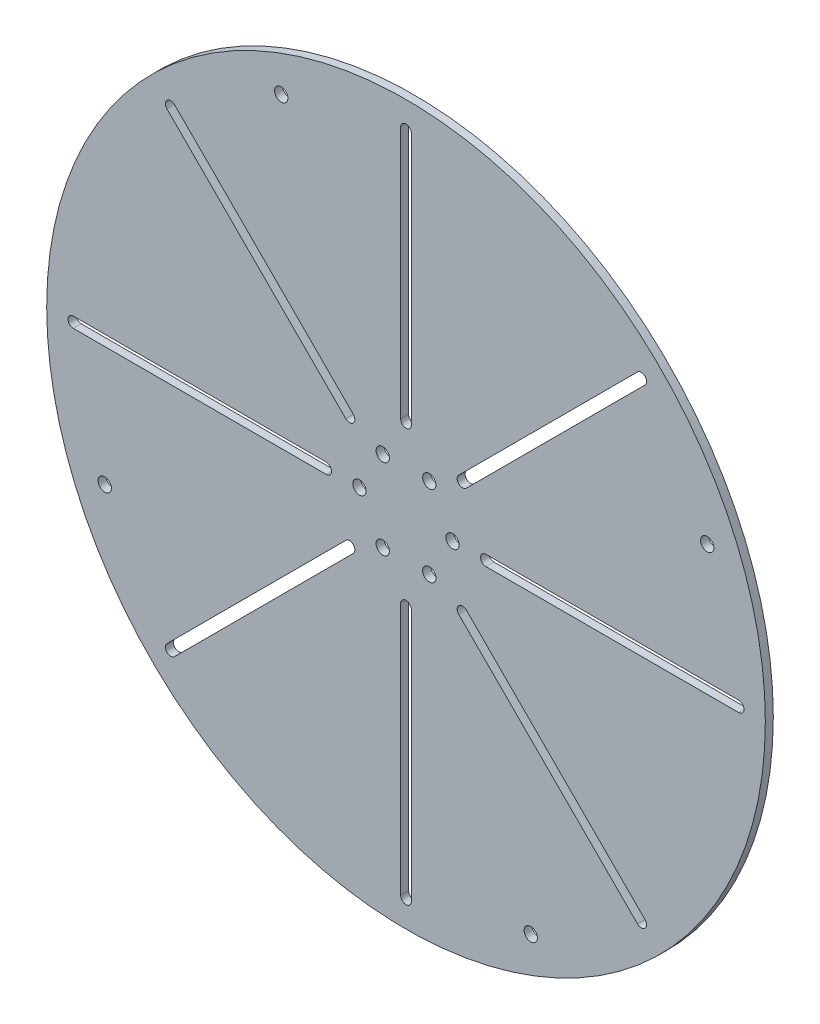
SolidWorks part; units mm, degrees
ref_plane "Front Plane" through (0, 0, 0) normal (0, 0, 1) x (1, 0, 0)
ref_plane "Top Plane" through (0, 0, 0) normal (0, 1, 0) x (1, 0, 0)
ref_plane "Right Plane" through (0, 0, 0) normal (1, 0, 0) x (0, 0, -1)
sketch "Sketch1" plane through (0, 0, 0) normal (0, 0, 1) x (1, 0, 0)
  line L0 (0, 0) -> (125, 0) construction
  line L1 (30, 0) -> (125, 0) construction
  line L2 (30, 2) -> (125, 2)
  line L3 (30, -2) -> (125, -2)
  line L4 (21.2132, -21.2132) -> (88.3883, -88.3883) construction
  line L5 (22.6274, -19.799) -> (89.8026, -86.9741)
  line L6 (19.799, -22.6274) -> (86.9741, -89.8026)
  line L7 (0, -30) -> (0, -125) construction
  line L8 (2, -30) -> (2, -125)
  line L9 (-2, -30) -> (-2, -125)
  line L10 (-21.2132, -21.2132) -> (-88.3883, -88.3883) construction
  line L11 (-19.799, -22.6274) -> (-86.9741, -89.8026)
  line L12 (-22.6274, -19.799) -> (-89.8026, -86.9741)
  line L13 (-30, 0) -> (-125, 0) construction
  line L14 (-30, -2) -> (-125, -2)
  line L15 (-30, 2) -> (-125, 2)
  line L16 (-21.2132, 21.2132) -> (-88.3883, 88.3883) construction
  line L17 (-22.6274, 19.799) -> (-89.8026, 86.9741)
  line L18 (-19.799, 22.6274) -> (-86.9741, 89.8026)
  line L19 (0, 30) -> (0, 125) construction
  line L20 (-2, 30) -> (-2, 125)
  line L21 (2, 30) -> (2, 125)
  line L22 (21.2132, 21.2132) -> (88.3883, 88.3883) construction
  line L23 (19.799, 22.6274) -> (86.9741, 89.8026)
  line L24 (22.6274, 19.799) -> (89.8026, 86.9741)
  line L25 (125, 0) -> (132.5, 0) construction
  line L26 (0, 0) -> (-47.8354, 115.4849) construction
  line L27 (0, 0) -> (0, -15) construction
  circle A0 centre (0, 0) radius 135
  circle A1 centre (0, 0) radius 132.5 construction
  circle A2 centre (0, 0) radius 30 construction
  circle A4 centre (0, 0) radius 125 construction
  arc A5 (30, 2) -> (30, -2) centre (30, 0) ccw
  arc A6 (125, -2) -> (125, 2) centre (125, 0) ccw
  arc A7 (22.6274, -19.799) -> (19.799, -22.6274) centre (21.2132, -21.2132) ccw
  arc A8 (86.9741, -89.8026) -> (89.8026, -86.9741) centre (88.3883, -88.3883) ccw
  arc A9 (2, -30) -> (-2, -30) centre (0, -30) ccw
  arc A10 (-2, -125) -> (2, -125) centre (0, -125) ccw
  arc A11 (-19.799, -22.6274) -> (-22.6274, -19.799) centre (-21.2132, -21.2132) ccw
  arc A12 (-89.8026, -86.9741) -> (-86.9741, -89.8026) centre (-88.3883, -88.3883) ccw
  arc A13 (-30, -2) -> (-30, 2) centre (-30, 0) ccw
  arc A14 (-125, 2) -> (-125, -2) centre (-125, 0) ccw
  arc A15 (-22.6274, 19.799) -> (-19.799, 22.6274) centre (-21.2132, 21.2132) ccw
  arc A16 (-86.9741, 89.8026) -> (-89.8026, 86.9741) centre (-88.3883, 88.3883) ccw
  arc A17 (-2, 30) -> (2, 30) centre (0, 30) ccw
  arc A18 (2, 125) -> (-2, 125) centre (0, 125) ccw
  arc A19 (19.799, 22.6274) -> (22.6274, 19.799) centre (21.2132, 21.2132) ccw
  arc A20 (89.8026, 86.9741) -> (86.9741, 89.8026) centre (88.3883, 88.3883) ccw
  circle A27 centre (0, 0) radius 17.5 construction
  circle A31 centre (-17.5, 0) radius 2.5
  circle A35 centre (-46.8787, 113.1752) radius 2.5
  circle A36 centre (113.1752, 46.8787) radius 2.5
  circle A37 centre (46.8787, -113.1752) radius 2.5
  circle A38 centre (0, 0) radius 23.5 construction
  circle A39 centre (-8.75, 15.1554) radius 2.5
  circle A40 centre (8.75, 15.1554) radius 2.5
  circle A41 centre (17.5, 0) radius 2.5
  circle A42 centre (8.75, -15.1554) radius 2.5
  circle A43 centre (-8.75, -15.1554) radius 2.5
  circle A44 centre (-113.1752, -46.8787) radius 2.5
  point P9 (77.5, 0)
  point P18 (54.8008, -54.8008)
  point P25 (0, -77.5)
  point P32 (-54.8008, -54.8008)
  point P39 (-77.5, 0)
  point P46 (-54.8008, 54.8008)
  point P53 (0, 77.5)
  point P60 (54.8008, 54.8008)
  point P65 (0, 0)
  point P78 (0, 0)
  point P84 (0, 0)
  point P85 (0, 0)
  point P86 (0, 0)
  point P93 (0, 0)
  point P95 (0, 0)
  point P99 (0, 0)
  dimension "D1" = 270
  dimension "D2" = 2.5
  dimension "D3" = 60
  dimension "D4" = 22.5
  dimension "D5" = 250
  dimension "D8" = 5
  dimension "D9" = 35
  dimension "D10" = 6
  dimension "D12" = 2.5
  dimension "D13" = 4
  dimension "D11" = 47
  dimension "D6" = 4
  dimension "D7" = 8
extrude "Boss-Extrude1" add sketch "Sketch1" along normal blind 3
